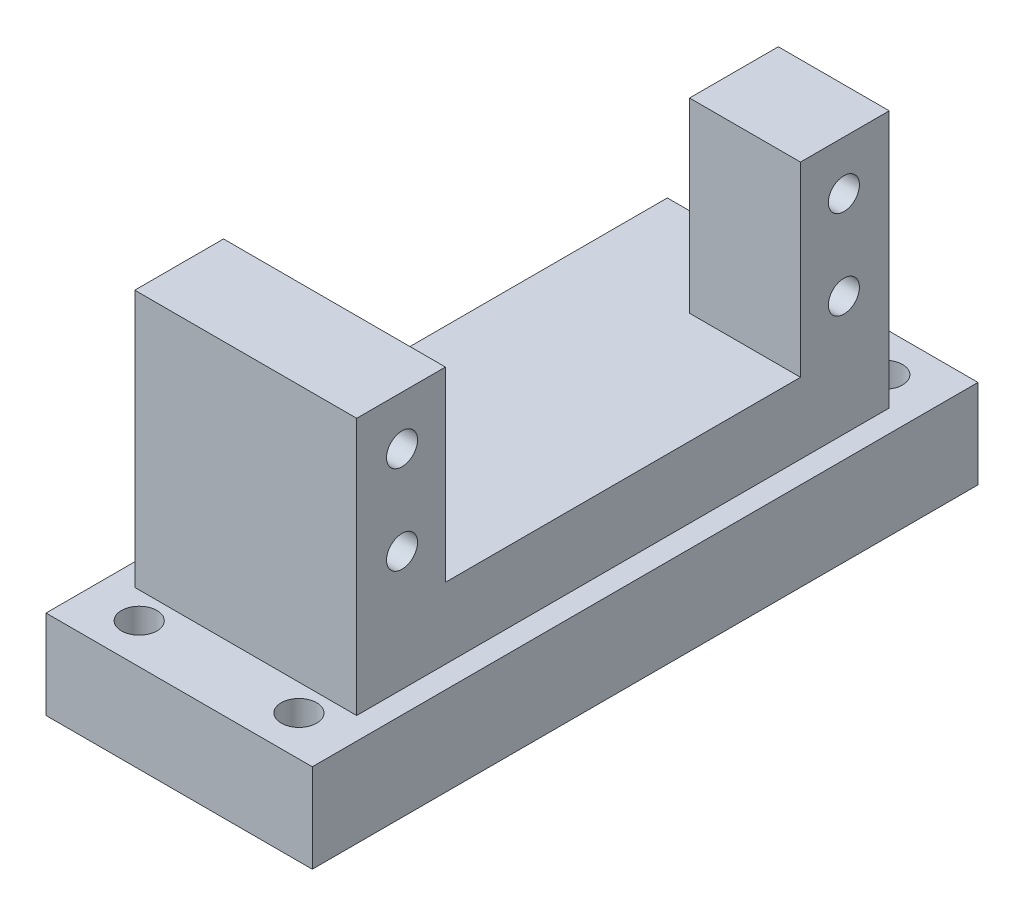
SolidWorks part; units mm, degrees
ref_plane "Front" through (0, 0, 0) normal (0, 0, 1) x (1, 0, 0)
ref_plane "Top" through (0, 0, 0) normal (0, 1, 0) x (1, 0, 0)
ref_plane "Right" through (0, 0, 0) normal (1, 0, 0) x (0, 0, -1)
sketch "Sketch1" plane through (0, 0, 0) normal (0, 1, 0) x (1, 0, 0)
  line L0 (12.5, 20) -> (-12.5, 20) construction
  line L1 (-12.5, -30) -> (12.5, -30)
  line L2 (-12.5, -30) -> (-12.5, 30)
  line L3 (-12.5, 30) -> (12.5, 30)
  line L4 (12.5, -30) -> (12.5, 30)
  line L5 (-12.5, -30) -> (12.5, 30) construction
  line L6 (-12.5, 30) -> (12.5, -30) construction
  line L7 (12.5, -20) -> (-12.5, -20) construction
  point P0 (0, 0)
  dimension "D1" = 60
  dimension "D2" = 25
  dimension "D3" = 10
  dimension "D4" = 10
extrude "Boss-Extrude1" add sketch "Sketch1" along normal blind 8
sketch "Sketch2" plane through (0, 8, 0) normal (0, 1, 0) x (1, 0, 0)
  line L0 (12.5, -30) -> (12.5, 30) construction
  line L1 (-12.5, -30) -> (12.5, -30)
  line L2 (-12.5, -30) -> (-12.5, -20)
  line L3 (-12.5, -20) -> (12.5, -20)
  line L4 (12.5, -30) -> (12.5, -20)
  line L5 (0, 30) -> (0, 20)
  line L6 (12.5, 20) -> (12.5, 30)
  line L10 (0, 20) -> (12.5, 20)
  line L11 (12.5, 30) -> (0, 30)
  dimension "D1" = 10
  dimension "D2" = 10
extrude "Boss-Extrude2" add sketch "Sketch2" along normal blind 21
sketch "Sketch3" plane through (12.5, 0, 0) normal (-1, 0, 0) x (0, 0, 1)
  line L6 (20, 29) -> (30, 29) construction
  circle A0 centre (-24.89, 23.47) radius 1.75
  circle A1 centre (-24.89, 13.47) radius 1.75
  circle A2 centre (24.89, 23.47) radius 1.75
  circle A3 centre (24.89, 13.47) radius 1.75
  dimension "D2" = 3.5
  dimension "D4" = 3.5
  dimension "D5" = 10
  dimension "D7" = 3.5
  dimension "D8" = 5.53
  dimension "D10" = 3.5
  dimension "D6" = 49.78
  dimension "D9" = 10
extrude "Cut-Extrude1" cut sketch "Sketch3" along normal up to next
sketch "Sketch6" plane through (0, 0, 0) normal (0, -1, 0) x (1, 0, 0)
  line L1 (15, 37.5) -> (-15, 37.5)
  line L2 (15, 37.5) -> (15, -37.5)
  line L3 (15, -37.5) -> (-15, -37.5)
  line L4 (-15, 37.5) -> (-15, -37.5)
  line L5 (15, 37.5) -> (-15, -37.5) construction
  line L6 (15, -37.5) -> (-15, 37.5) construction
  point P0 (0, 0)
  dimension "D1" = 30
  dimension "D2" = 75
extrude "Boss-Extrude3" add sketch "Sketch6" along normal blind 10
sketch "Sketch7" plane through (0, 0, 0) normal (0, 1, 0) x (1, 0, 0)
  circle A0 centre (9, 33) radius 2
  circle A1 centre (-9, 33) radius 2
  circle A2 centre (-9, -33) radius 2
  circle A3 centre (9, -33) radius 2
  dimension "D1" = 4
  dimension "D5" = 2
  dimension "D2" = 9
  dimension "D4" = 33
  dimension "D3" = 2
extrude "Cut-Extrude4" cut sketch "Sketch7" against normal up to next
